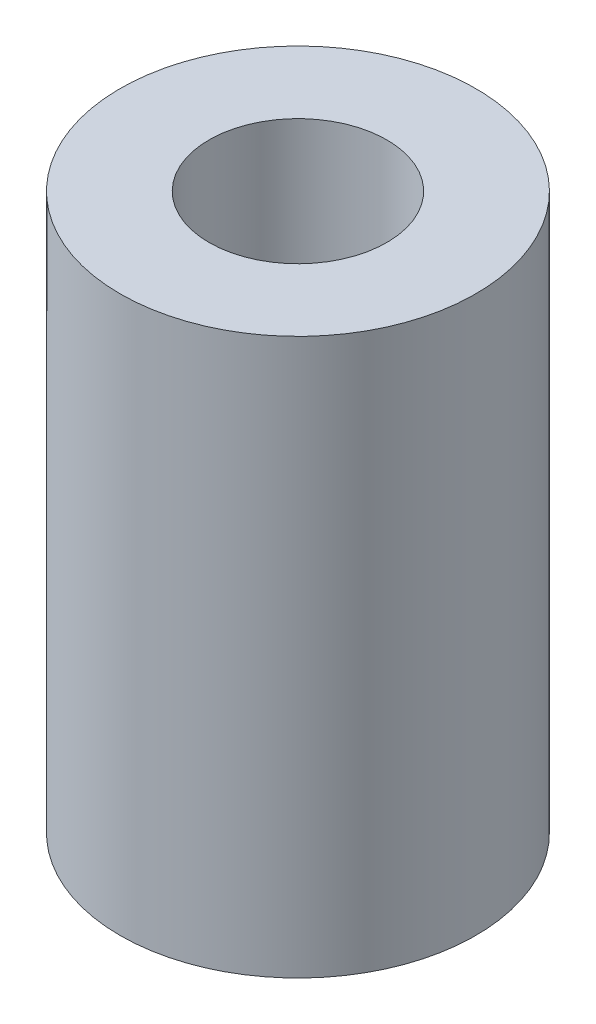
SolidWorks part; units mm, degrees
ref_plane "Front Plane" through (0, 0, 0) normal (0, 0, 1) x (1, 0, 0)
ref_plane "Top Plane" through (0, 0, 0) normal (0, 1, 0) x (1, 0, 0)
ref_plane "Right Plane" through (0, 0, 0) normal (1, 0, 0) x (0, 0, -1)
sketch "Sketch1" plane through (0, 0, 0) normal (0, 1, 0) x (1, 0, 0)
  circle A0 centre (0, 0) radius 8
  circle A1 centre (0, 0) radius 4
  dimension "D1" = 16
  dimension "D2" = 8
extrude "Boss-Extrude1" add sketch "Sketch1" along normal blind 25
